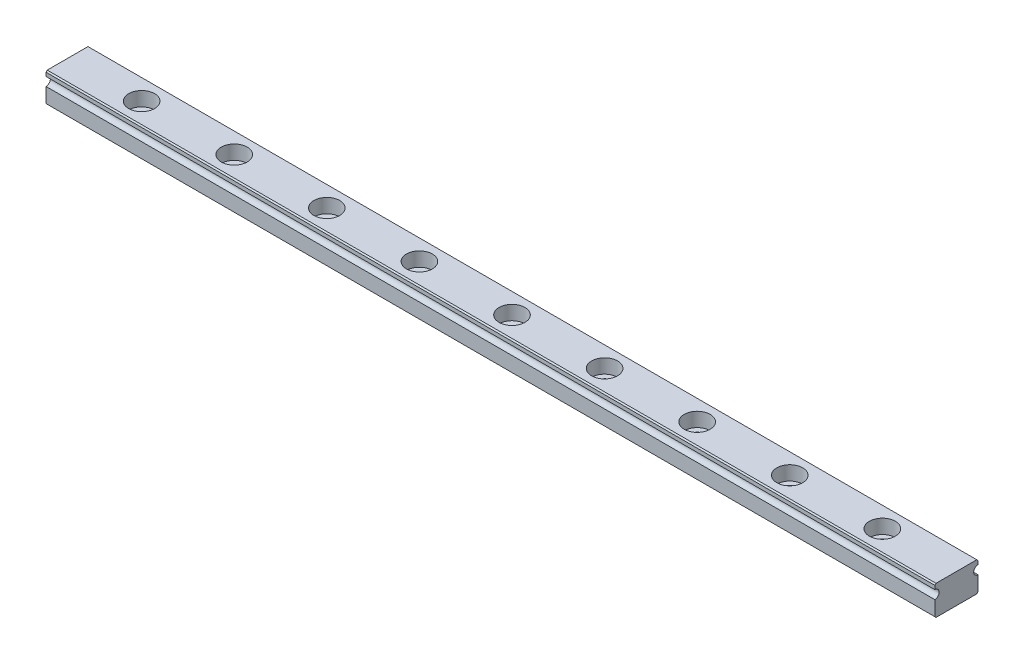
SolidWorks part; units mm, degrees
material "铸造合金钢"
ref_plane "前视基准面" through (0, 0, 0) normal (0, 0, 1) x (1, 0, 0)
ref_plane "上视基准面" through (0, 0, 0) normal (0, 1, 0) x (1, 0, 0)
ref_plane "右视基准面" through (0, 0, 0) normal (1, 0, 0) x (0, 0, -1)
sketch "草图1" plane through (0, 0, 0) normal (1, 0, 0) x (0, 0, -1)
  line L0 (0, 0) -> (0, 3.6487) construction
  line L1 (0, 0) -> (3.5451, 0) construction
  line L2 (3.498, 0.202) -> (3.498, -2.198)
  line L3 (3.498, -2.198) -> (3.3, -2.396)
  line L4 (3.3, -2.396) -> (-3.3, -2.396)
  line L5 (-3.3, 2.4) -> (3.3, 2.4)
  line L6 (3.3, 2.4) -> (3.498, 2.202)
  line L7 (3.498, 2.202) -> (3.498, 1.602)
  line L8 (-3.498, -2.198) -> (-3.3, -2.396)
  line L9 (-3.498, 0.202) -> (-3.498, -2.198)
  line L10 (-3.498, 2.202) -> (-3.498, 1.602)
  line L11 (-3.3, 2.4) -> (-3.498, 2.202)
  arc A0 (3.498, 1.602) -> (3.498, 0.202) centre (3.498, 0.902) ccw
  arc A1 (-3.498, 1.602) -> (-3.498, 0.202) centre (-3.498, 0.902) cw
  circle A2 centre (0, 0) radius 4.5 construction
  point P17 (0, -2.396)
  point P23 (0, 2.4)
  dimension "D2" = 0.7
  dimension "D10" = 9
  dimension "D1" = 3.3
  dimension "D3" = 2.4
  dimension "D4" = 0.6
  dimension "D5" = 0.28
  dimension "D6" = 135
  dimension "D7" = 0.28
  dimension "D8" = 135
  dimension "D9" = 2.4
extrude "凸台-拉伸1" add sketch "草图1" along normal blind 144
sketch "草图2" plane through (0, 2.4, 0) normal (0, 1, 0) x (1, 0, 0)
  line L0 (0, 0) -> (-4.1171, 0) construction
  line L1 (0, 3.3) -> (0, -3.3) construction
  circle A0 centre (12, 0) radius 2.1
  circle A1 centre (27, 0) radius 2.1
  circle A2 centre (42, 0) radius 2.1
  circle A3 centre (57, 0) radius 2.1
  circle A4 centre (72, 0) radius 2.1
  circle A5 centre (87, 0) radius 2.1
  circle A6 centre (102, 0) radius 2.1
  circle A7 centre (117, 0) radius 2.1
  circle A8 centre (132, 0) radius 2.1
  circle A9 centre (147, 0) radius 2.1
  circle A10 centre (162, 0) radius 2.1
  circle A11 centre (177, 0) radius 2.1
  circle A12 centre (192, 0) radius 2.1
  circle A13 centre (207, 0) radius 2.1
  circle A14 centre (222, 0) radius 2.1
  dimension "D1" = 4.2
  dimension "D2" = 12
  dimension "D3" = 15
extrude "切除-拉伸1" cut sketch "草图2" against normal blind 2.3
sketch "草图3" plane through (0, 2.4, 0) normal (0, 1, 0) x (1, 0, 0)
  circle A0 centre (12, 0) radius 1.2
  circle A1 centre (12, 0) radius 2.1 construction
  circle A2 centre (27, 0) radius 1.2
  circle A3 centre (42, 0) radius 1.2
  circle A4 centre (57, 0) radius 1.2
  circle A5 centre (72, 0) radius 1.2
  circle A6 centre (87, 0) radius 1.2
  circle A7 centre (102, 0) radius 1.2
  circle A8 centre (117, 0) radius 1.2
  circle A9 centre (132, 0) radius 1.2
  circle A10 centre (147, 0) radius 1.2
  circle A11 centre (162, 0) radius 1.2
  circle A12 centre (177, 0) radius 1.2
  circle A13 centre (192, 0) radius 1.2
  circle A14 centre (207, 0) radius 1.2
  circle A15 centre (222, 0) radius 1.2
  dimension "D1" = 2.4
  dimension "D2" = 15
extrude "切除-拉伸2" cut sketch "草图3" against normal through all both and the other way through all
